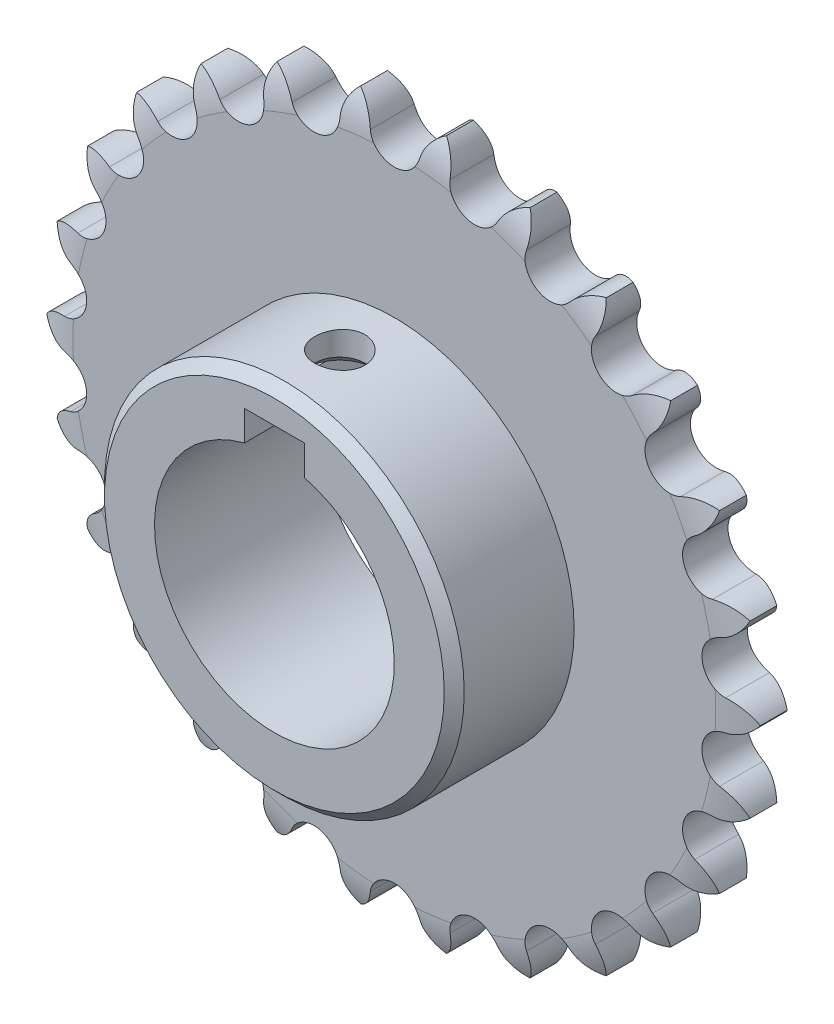
SolidWorks part; units mm, degrees
material "Plain Carbon Steel"
ref_plane "Front Plane" through (0, 0, 0) normal (0, 0, 1) x (1, 0, 0)
ref_plane "Top Plane" through (0, 0, 0) normal (0, 1, 0) x (1, 0, 0)
ref_plane "Right Plane" through (0, 0, 0) normal (1, 0, 0) x (0, 0, -1)
sketch "Sketch2" plane through (0, 0, 0) normal (0, 0, 1) x (1, 0, 0)
  line L0 (0, 53.2892) -> (0, 0) construction
  line L1 (0, 0) -> (9.6217, 51.1475) construction
  circle A0 centre (0, 0) radius 52.0446 construction
  circle A1 centre (0, 0) radius 53.2892 construction
  circle A2 centre (0, 0) radius 56.7055 construction
  arc A3 (-3.9297, 52.4145) -> (3.9297, 52.4145) centre (0, 53.2892) ccw
  arc A4 (6.8687, 56.288) -> (3.9297, 52.4145) centre (9.6217, 51.1475) ccw
  arc A5 (-6.8687, 56.288) -> (-3.9297, 52.4145) centre (-9.6217, 51.1475) cw
  arc A6 (6.8015, 56.2961) -> (8.7281, 51.8318) centre (2.8983, 51.9638) cw
  arc A7 (8.7281, 51.8318) -> (16.3591, 49.951) centre (12.7529, 51.7407) ccw
  arc A8 (20.1397, 53.0086) -> (16.3591, 49.951) centre (21.5825, 47.3586) ccw
  arc A9 (20.0764, 53.0326) -> (20.8786, 48.2369) centre (15.2499, 49.7602) cw
  arc A10 (20.8786, 48.2369) -> (27.8378, 44.5845) centre (24.7647, 47.1852) ccw
  arc A11 (32.2402, 46.6485) -> (27.8378, 44.5845) centre (32.289, 40.8174) ccw
  arc A12 (32.1845, 46.6869) -> (31.8158, 41.8387) centre (26.7151, 44.6648) cw
  arc A13 (31.8158, 41.8387) -> (37.6987, 36.6269) centre (35.3373, 39.8875) ccw
  arc A14 (42.4671, 37.5774) -> (37.6987, 36.6269) centre (41.119, 31.9041) ccw
  arc A15 (42.4222, 37.628) -> (40.9039, 33.0089) centre (36.6278, 36.9736) cw
  arc A16 (40.9039, 33.0089) -> (45.3686, 26.5407) centre (43.8562, 30.2717) ccw
  arc A17 (50.2259, 26.3224) -> (45.3686, 26.5407) centre (47.5593, 21.1366) ccw
  arc A18 (50.1945, 26.3823) -> (47.6149, 22.2608) centre (44.4118, 27.1336) cw
  arc A19 (47.6149, 22.2608) -> (50.4019, 14.9121) centre (49.8263, 18.8966) ccw
  arc A20 (55.0658, 13.5376) -> (50.4019, 14.9121) centre (51.2356, 9.1407) ccw
  arc A21 (55.0496, 13.6034) -> (51.5586, 10.2189) centre (49.6148, 15.7167) cw
  arc A22 (51.5586, 10.2189) -> (52.506, 2.4168) centre (52.9007, 6.4233) ccw
  arc A23 (56.7055, -0.0338) -> (52.506, 2.4168) centre (51.9343, -3.3864) ccw
  arc A24 (56.7055, 0.0338) -> (52.506, -2.4168) centre (51.9343, 3.3864) cw
  arc A25 (52.506, -2.4168) -> (51.5586, -10.2189) centre (52.9007, -6.4233) ccw
  arc A26 (55.0496, -13.6034) -> (51.5586, -10.2189) centre (49.6148, -15.7167) ccw
  arc A27 (55.0658, -13.5376) -> (50.4019, -14.9121) centre (51.2356, -9.1407) cw
  arc A28 (50.4019, -14.9121) -> (47.6149, -22.2608) centre (49.8263, -18.8966) ccw
  arc A29 (50.1945, -26.3823) -> (47.6149, -22.2608) centre (44.4118, -27.1336) ccw
  arc A30 (50.2259, -26.3224) -> (45.3686, -26.5407) centre (47.5593, -21.1366) cw
  arc A31 (45.3686, -26.5407) -> (40.9039, -33.0089) centre (43.8562, -30.2717) ccw
  arc A32 (42.4222, -37.628) -> (40.9039, -33.0089) centre (36.6278, -36.9736) ccw
  arc A33 (42.4671, -37.5774) -> (37.6987, -36.6269) centre (41.119, -31.9041) cw
  arc A34 (37.6987, -36.6269) -> (31.8158, -41.8387) centre (35.3373, -39.8875) ccw
  arc A35 (32.1845, -46.6869) -> (31.8158, -41.8387) centre (26.7151, -44.6648) ccw
  arc A36 (32.2402, -46.6485) -> (27.8378, -44.5845) centre (32.289, -40.8174) cw
  arc A37 (27.8378, -44.5845) -> (20.8786, -48.2369) centre (24.7647, -47.1852) ccw
  arc A38 (20.0764, -53.0326) -> (20.8786, -48.2369) centre (15.2499, -49.7602) ccw
  arc A39 (20.1397, -53.0086) -> (16.3591, -49.951) centre (21.5825, -47.3586) cw
  arc A40 (16.3591, -49.951) -> (8.7281, -51.8318) centre (12.7529, -51.7407) ccw
  arc A41 (6.8015, -56.2961) -> (8.7281, -51.8318) centre (2.8983, -51.9638) ccw
  arc A42 (6.8687, -56.288) -> (3.9297, -52.4145) centre (9.6217, -51.1475) cw
  arc A43 (3.9297, -52.4145) -> (-3.9297, -52.4145) centre (0, -53.2892) ccw
  arc A44 (-6.8687, -56.288) -> (-3.9297, -52.4145) centre (-9.6217, -51.1475) ccw
  arc A45 (-6.8015, -56.2961) -> (-8.7281, -51.8318) centre (-2.8983, -51.9638) cw
  arc A46 (-8.7281, -51.8318) -> (-16.3591, -49.951) centre (-12.7529, -51.7407) ccw
  arc A47 (-20.1397, -53.0086) -> (-16.3591, -49.951) centre (-21.5825, -47.3586) ccw
  arc A48 (-20.0764, -53.0326) -> (-20.8786, -48.2369) centre (-15.2499, -49.7602) cw
  arc A49 (-20.8786, -48.2369) -> (-27.8378, -44.5845) centre (-24.7647, -47.1852) ccw
  arc A50 (-32.2402, -46.6485) -> (-27.8378, -44.5845) centre (-32.289, -40.8174) ccw
  arc A51 (-32.1845, -46.6869) -> (-31.8158, -41.8387) centre (-26.7151, -44.6648) cw
  arc A52 (-31.8158, -41.8387) -> (-37.6987, -36.6269) centre (-35.3373, -39.8875) ccw
  arc A53 (-42.4671, -37.5774) -> (-37.6987, -36.6269) centre (-41.119, -31.9041) ccw
  arc A54 (-42.4222, -37.628) -> (-40.9039, -33.0089) centre (-36.6278, -36.9736) cw
  arc A55 (-40.9039, -33.0089) -> (-45.3686, -26.5407) centre (-43.8562, -30.2717) ccw
  arc A56 (-50.2259, -26.3224) -> (-45.3686, -26.5407) centre (-47.5593, -21.1366) ccw
  arc A57 (-50.1945, -26.3823) -> (-47.6149, -22.2608) centre (-44.4118, -27.1336) cw
  arc A58 (-47.6149, -22.2608) -> (-50.4019, -14.9121) centre (-49.8263, -18.8966) ccw
  arc A59 (-55.0658, -13.5376) -> (-50.4019, -14.9121) centre (-51.2356, -9.1407) ccw
  arc A60 (-55.0496, -13.6034) -> (-51.5586, -10.2189) centre (-49.6148, -15.7167) cw
  arc A61 (-51.5586, -10.2189) -> (-52.506, -2.4168) centre (-52.9007, -6.4233) ccw
  arc A62 (-56.7055, 0.0338) -> (-52.506, -2.4168) centre (-51.9343, 3.3864) ccw
  arc A63 (-56.7055, -0.0338) -> (-52.506, 2.4168) centre (-51.9343, -3.3864) cw
  arc A64 (-52.506, 2.4168) -> (-51.5586, 10.2189) centre (-52.9007, 6.4233) ccw
  arc A65 (-55.0496, 13.6034) -> (-51.5586, 10.2189) centre (-49.6148, 15.7167) ccw
  arc A66 (-55.0658, 13.5376) -> (-50.4019, 14.9121) centre (-51.2356, 9.1407) cw
  arc A67 (-50.4019, 14.9121) -> (-47.6149, 22.2608) centre (-49.8263, 18.8966) ccw
  arc A68 (-50.1945, 26.3823) -> (-47.6149, 22.2608) centre (-44.4118, 27.1336) ccw
  arc A69 (-50.2259, 26.3224) -> (-45.3686, 26.5407) centre (-47.5593, 21.1366) cw
  arc A70 (-45.3686, 26.5407) -> (-40.9039, 33.0089) centre (-43.8562, 30.2717) ccw
  arc A71 (-42.4222, 37.628) -> (-40.9039, 33.0089) centre (-36.6278, 36.9736) ccw
  arc A72 (-42.4671, 37.5774) -> (-37.6987, 36.6269) centre (-41.119, 31.9041) cw
  arc A73 (-37.6987, 36.6269) -> (-31.8158, 41.8387) centre (-35.3373, 39.8875) ccw
  arc A74 (-32.1845, 46.6869) -> (-31.8158, 41.8387) centre (-26.7151, 44.6648) ccw
  arc A75 (-32.2402, 46.6485) -> (-27.8378, 44.5845) centre (-32.289, 40.8174) cw
  arc A76 (-27.8378, 44.5845) -> (-20.8786, 48.2369) centre (-24.7647, 47.1852) ccw
  arc A77 (-20.0764, 53.0326) -> (-20.8786, 48.2369) centre (-15.2499, 49.7602) ccw
  arc A78 (-20.1397, 53.0086) -> (-16.3591, 49.951) centre (-21.5825, 47.3586) cw
  arc A79 (-16.3591, 49.951) -> (-8.7281, 51.8318) centre (-12.7529, 51.7407) ccw
  arc A80 (-6.8015, 56.2961) -> (-8.7281, 51.8318) centre (-2.8983, 51.9638) ccw
  circle A81 centre (0, 0) radius 19.05
  point P190 (0, 0)
  dimension "D1" = 113.411
  dimension "D2" = 106.5784
  dimension "D3" = 104.0892
  dimension "D4" = 8.0518
  dimension "D5" = 11.6625
  dimension "D7" = 38.1
  dimension "D6" = 26
extrude "Boss-Extrude1" add sketch "Sketch2" along normal blind 7.2136 contours A5 A80 A79 A78 A77 A76 A75 A74 A73 A72 A71 A70 A69 A68 A67 A66 A65 A64 A63 A62 A61 A60 A59 A58 A57 A56 A55 A54 A53 A52 A51 A50 A49 A48 A47 A46 A45 A44 A43 A42 A41 A40 A39 A38 A37 A36 A35 A34 A33 A32 A31
sketch "Sketch3" plane through (0, 0, 0) normal (1, 0, 0) x (0, 0, -1)
  line L0 (0, 0) -> (-69.5556, 0) construction
  line L1 (-7.2136, 37.5868) -> (-7.2136, 33.0089) construction
  line L2 (-7.2136, 28.575) -> (-26.2636, 28.575)
  line L3 (-7.2136, 28.575) -> (-7.2136, 19.05)
  line L4 (-7.2136, 19.05) -> (-26.2636, 19.05)
  line L5 (-26.2636, 28.575) -> (-26.2636, 19.05)
  dimension "D1" = 19.05
  dimension "D2" = 38.1
  dimension "D3" = 57.15
revolve "Revolve1" add sketch "Sketch3" angle 360 about L0
sketch "Sketch4" plane through (0, 0, 26.2636) normal (0, 0, 1) x (1, 0, 0)
  line L0 (0, 0) -> (0, 28.575) construction
  line L2 (-4.7625, 18.4451) -> (4.7625, 18.4451)
  line L3 (-4.7625, 18.4451) -> (-4.7625, 23.2076)
  line L4 (-4.7625, 23.2076) -> (4.7625, 23.2076)
  line L5 (4.7625, 18.4451) -> (4.7625, 23.2076)
  circle A0 centre (0, 0) radius 28.575 construction
  circle A1 centre (0, 0) radius 19.05 construction
  dimension "D1" = 9.525
  dimension "D2" = 4.7625
extrude "Cut-Extrude1" cut sketch "Sketch4" against normal through all
hole_wizard "3/8-16 Tapped Hole2" positions "Sketch10" profile "Sketch11" tap size "3/8-16" standard "ANSI Inch"
sketch "Sketch10" plane through (0, 23.2076, 0) normal (0, -1, 0) x (-1, 0, 0)
  point P0 (0, -15.875)
  dimension "D1" = 15.875
sketch "Sketch11" plane through (0, 23.2076, 15.875) normal (1, 0, 0) x (0, 0, -1)
  line L0 (0, 0) -> (0, 9.4967)
  line L1 (0, 9.4967) -> (3.9687, 7.112)
  line L2 (3.9687, 7.112) -> (3.9687, 1.4288)
  line L3 (3.9687, 1.4288) -> (5.3975, 0)
  line L5 (5.3975, 0) -> (0, 0)
  line L6 (-3.9687, 1.4288) -> (-5.3975, 0) construction
  line L10 (0, 9.4967) -> (-3.9687, 7.112) construction
  line L11 (0, -6.35) -> (0, 107.95) construction
  dimension "Tap Drill Dia." = 7.9375
  dimension "Tap Drill Depth" = 7.112
  dimension "Near C'Sink Dia." = 10.795
  dimension "Near C'Sink Angle" = 90
  dimension "Drill Angle" = 118
cosmetic thread "Hole Thread2" parameters "D1"=5.3674, "D2"=9.525
sketch "Sketch12" plane through (0, 0, 0) normal (1, 0, 0) x (0, 0, -1)
  line L0 (-3.6068, 56.2683) -> (-3.6068, 34.7664) construction
  line L1 (-7.2136, 56.2683) -> (0, 56.2683) construction
  line L2 (-5.6261, 56.8894) -> (-5.6261, 34.7614) construction
  line L3 (-7.2136, 56.2683) -> (-7.2136, 51.8318) construction
  line L4 (-7.2136, 50.419) -> (-7.9756, 50.419)
  line L5 (-7.2136, 46.648) -> (-7.2136, 41.8387) construction
  line L6 (-7.9756, 50.419) -> (-7.9756, 56.896)
  line L7 (-7.9756, 56.896) -> (-5.6261, 56.896)
  line L8 (0, 0) -> (-64.738, 0) construction
  line L9 (0, 50.419) -> (0.762, 50.419)
  line L10 (0.762, 50.419) -> (0.762, 56.896)
  line L11 (0.762, 56.896) -> (-1.5875, 56.896)
  arc A0 (-5.6261, 56.896) -> (-7.2136, 50.419) centre (5.4823, 50.7403) ccw
  arc A1 (-1.5875, 56.896) -> (0, 50.419) centre (-12.6959, 50.7403) cw
  dimension "D2" = 12.7
  dimension "D1" = 1.5875
  dimension "D3" = 0.762
  dimension "D4" = 50.419
  dimension "D5" = 56.896
revolve "Cut-Revolve1" cut sketch "Sketch12" angle 360 about L8
chamfer "Chamfer1" distance 1.5875 angle 45 1 edges at (-28.575, 0, 26.2636)
